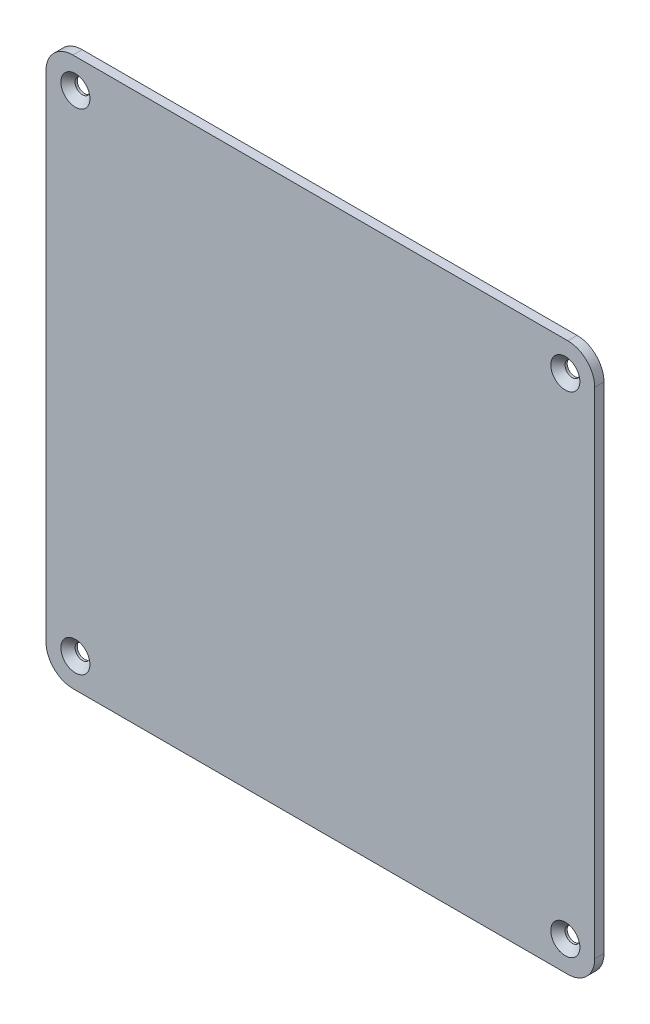
SolidWorks part; units mm, degrees
ref_plane "Piano frontale" through (0, 0, 0) normal (0, 0, 1) x (1, 0, 0)
ref_plane "Piano superiore" through (0, 0, 0) normal (0, 1, 0) x (1, 0, 0)
ref_plane "Piano destro" through (0, 0, 0) normal (1, 0, 0) x (0, 0, -1)
sketch "Sketch1" plane through (0, 0, 0) normal (0, 0, 1) x (1, 0, 0)
  line L8 (-88.7, 80) -> (-88.7, -80)
  line L9 (-80, -88.7) -> (80, -88.7)
  line L10 (88.7, -80) -> (88.7, 80)
  line L11 (80, 88.7) -> (-80, 88.7)
  arc A8 (-80, 88.7) -> (-88.7, 80) centre (-80, 80) ccw
  arc A9 (-88.7, -80) -> (-80, -88.7) centre (-80, -80) ccw
  arc A10 (80, -88.7) -> (88.7, -80) centre (80, -80) ccw
  arc A11 (88.7, 80) -> (80, 88.7) centre (80, 80) ccw
extrude "Boss-Extrude1" add sketch "Sketch1" against normal blind 3
hole_wizard "CSK for M4 Flat Head Machine Screw1" positions "Sketch2" profile "Sketch3" countersink size "M4" standard "ANSI Metric" end condition through all
sketch "Sketch2" plane through (0, 0, 0) normal (0, 0, 1) x (1, 0, 0)
  point P0 (-79.2, 79.2)
  point P3 (79.2, 79.2)
  point P6 (79.2, -79.2)
  point P9 (-79.2, -79.2)
sketch "Sketch3" plane through (-79.2, 79.2, 0) normal (1, 0, 0) x (0, -1, 0)
  line L0 (0, 0) -> (0, 3)
  line L1 (0, 3) -> (2.4, 3)
  line L2 (2.4, 3) -> (2.4, 2.3)
  line L3 (2.4, 2.3) -> (4.7, 0)
  line L5 (4.7, 0) -> (0, 0)
  line L6 (-2.4, 2.3) -> (-4.7, 0) construction
  line L11 (0, -6.35) -> (0, 107.95) construction
  dimension "Thru Hole Dia." = 4.8
  dimension "Thru Hole Depth" = 3
  dimension "Near C'Sink Dia." = 9.4
  dimension "Near C'Sink Angle" = 90
